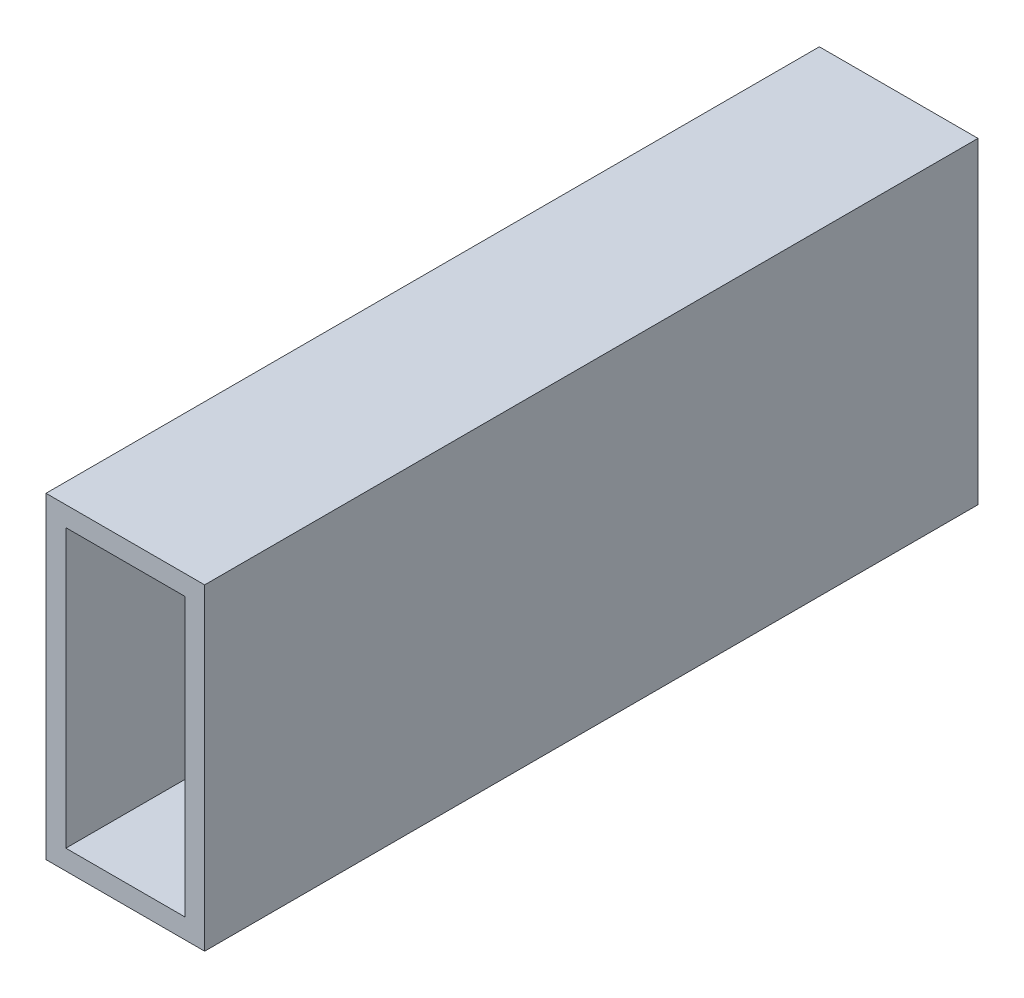
SolidWorks part; units mm, degrees
ref_plane "Front Plane" through (0, 0, 0) normal (0, 0, 1) x (1, 0, 0)
ref_plane "Top Plane" through (0, 0, 0) normal (0, 1, 0) x (1, 0, 0)
ref_plane "Right Plane" through (0, 0, 0) normal (1, 0, 0) x (0, 0, -1)
sketch "Sketch1" plane through (0, 0, 0) normal (0, 0, 1) x (1, 0, 0)
  line L1 (-12.7, -25.4) -> (12.7, -25.4)
  line L2 (-12.7, -25.4) -> (-12.7, 25.4)
  line L3 (-12.7, 25.4) -> (12.7, 25.4)
  line L4 (12.7, -25.4) -> (12.7, 25.4)
  line L5 (-12.7, -25.4) -> (12.7, 25.4) construction
  line L6 (-12.7, 25.4) -> (12.7, -25.4) construction
  point P0 (0, 0)
  dimension "D1" = 25.4
  dimension "D2" = 50.8
extrude "Boss-Extrude1" add sketch "Sketch1" along normal mid plane 123.825
shell "Shell1" thickness 3.175
